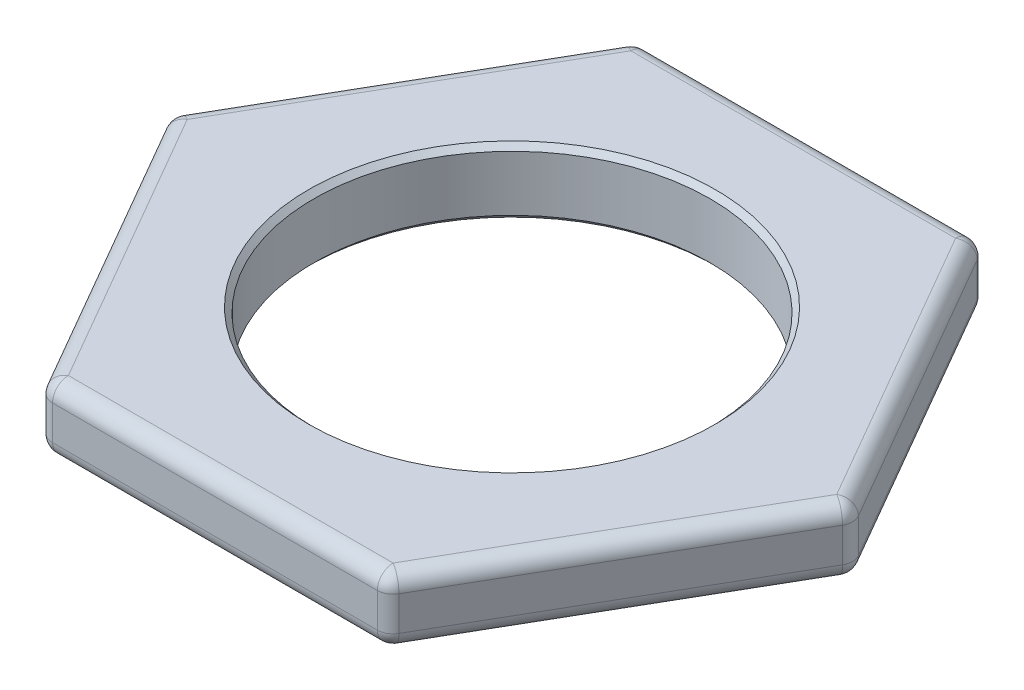
SolidWorks part; units mm, degrees
ref_plane "Front Plane" through (0, 0, 0) normal (0, 0, 1) x (1, 0, 0)
ref_plane "Top Plane" through (0, 0, 0) normal (0, 1, 0) x (1, 0, 0)
ref_plane "Right Plane" through (0, 0, 0) normal (1, 0, 0) x (0, 0, -1)
sketch "Sketch1" plane through (0, 0, 0) normal (0, 1, 0) x (1, 0, 0)
  line L1 (-8.2489, -14.2875) -> (8.2489, -14.2875)
  line L2 (8.2489, -14.2875) -> (16.4978, 0)
  line L3 (16.4978, 0) -> (8.2489, 14.2875)
  line L4 (8.2489, 14.2875) -> (-8.2489, 14.2875)
  line L5 (-8.2489, 14.2875) -> (-16.4978, 0)
  line L6 (-16.4978, 0) -> (-8.2489, -14.2875)
  circle A0 centre (0, 0) radius 14.2875 construction
  circle A1 centre (0, 0) radius 9.525
  dimension "D2" = 19.05
  dimension "D1" = 28.575
extrude "Boss-Extrude1" add sketch "Sketch1" along normal blind 3.175
chamfer "Chamfer1" distance 0.254 angle 45 2 edges at (0, 0, 9.525) (0, 3.175, 9.525)
fillet "Fillet1" radius 0.762 18 edges at (-16.4978, 1.5875, 0) (-12.3733, 3.175, 7.1437) (-12.3733, 0, 7.1437) (-12.3733, 0, -7.1438) (-12.3733, 3.175, -7.1438) (-8.2489, 1.5875, -14.2875) (0, 0, -14.2875) (0, 3.175, -14.2875) (8.2489, 1.5875, -14.2875) (12.3733, 0, -7.1438) (12.3733, 3.175, -7.1438) (16.4978, 1.5875, 0) (8.2489, 1.5875, 14.2875) (12.3733, 0, 7.1438) (12.3733, 3.175, 7.1438) (-8.2489, 1.5875, 14.2875) (0, 0, 14.2875) (0, 3.175, 14.2875)
